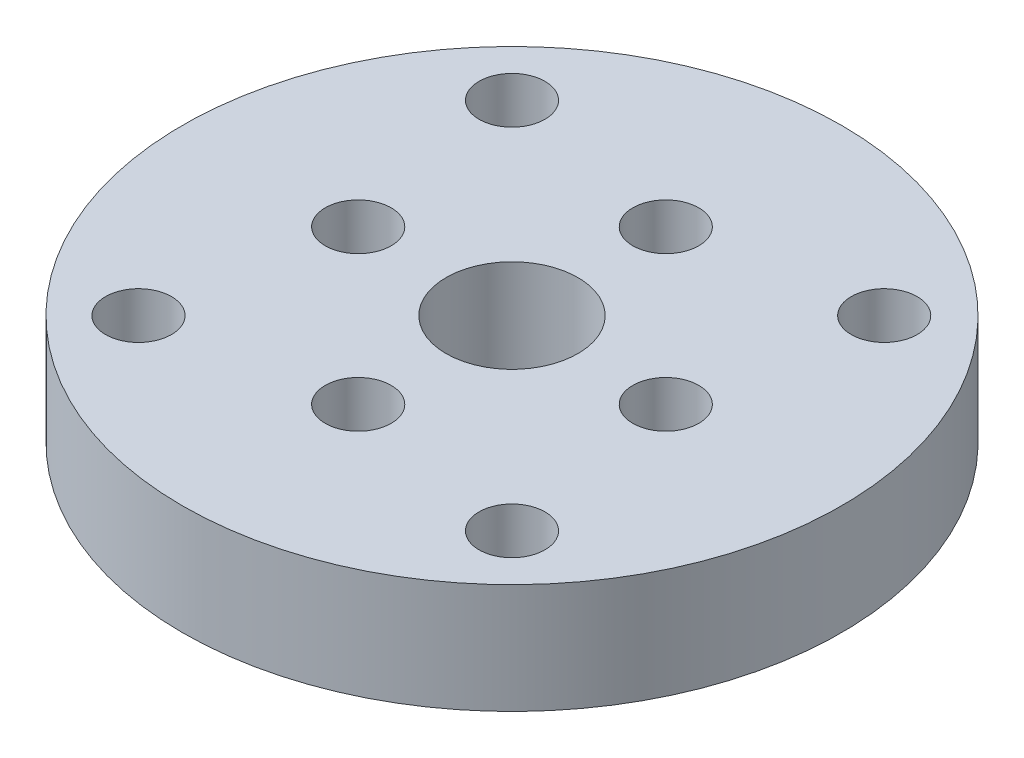
SolidWorks part; units mm, degrees
ref_plane "Front Plane" through (0, 0, 0) normal (0, 0, 1) x (1, 0, 0)
ref_plane "Top Plane" through (0, 0, 0) normal (0, 1, 0) x (1, 0, 0)
ref_plane "Right Plane" through (0, 0, 0) normal (1, 0, 0) x (0, 0, -1)
sketch "Sketch1" plane through (0, 0, 0) normal (0, 1, 0) x (1, 0, 0)
  circle A0 centre (0, 0) radius 15
extrude "Boss-Extrude1" add sketch "Sketch1" along normal blind 5
sketch "Sketch3" plane through (0, 0, 0) normal (0, -1, 0) x (1, 0, 0)
  line L0 (8.4706, -8.4706) -> (-8.5, 8.5) construction
  line L1 (-8.4853, -8.4853) -> (8.4853, 8.4853) construction
  circle A1 centre (-8.5, 8.5) radius 1.5
  circle A3 centre (8.4853, 8.4853) radius 1.5
  circle A5 centre (-8.4853, -8.4853) radius 1.5
  circle A7 centre (8.4706, -8.4706) radius 1.5
  point P6 (0, 0)
extrude "Cut-Extrude2" cut sketch "Sketch3" against normal blind 5
sketch "Sketch4" plane through (0, 5, 0) normal (0, 1, 0) x (1, 0, 0)
  line L0 (7, 0) -> (-7, 0) construction
  line L1 (0, 7) -> (0, -7) construction
  circle A0 centre (7, 0) radius 1.5
  circle A1 centre (0, -7) radius 1.5
  circle A2 centre (-7, 0) radius 1.5
  circle A3 centre (0, 7) radius 1.5
  point P14 (0, 0)
  point P17 (0, 0)
extrude "Cut-Extrude3" cut sketch "Sketch4" against normal blind 5
sketch "Sketch5" plane through (0, 5, 0) normal (0, 1, 0) x (1, 0, 0)
  circle A0 centre (0, 0) radius 3
extrude "Cut-Extrude4" cut sketch "Sketch5" against normal blind 10
